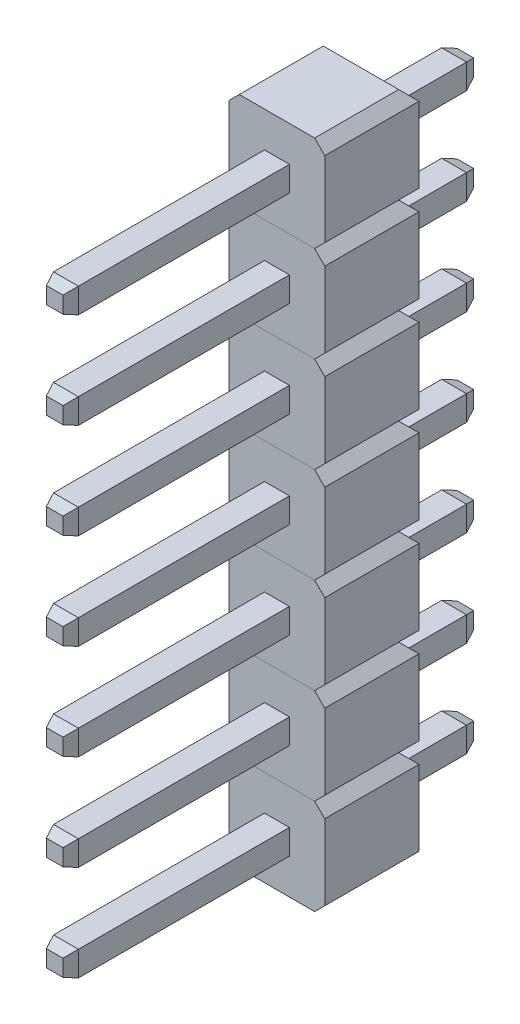
SolidWorks part; units mm, degrees
ref_plane "Front" through (0, 0, 0) normal (0, 0, 1) x (1, 0, 0)
ref_plane "Top" through (0, 0, 0) normal (0, 1, 0) x (1, 0, 0)
ref_plane "Right" through (0, 0, 0) normal (1, 0, 0) x (0, 0, -1)
sketch "Sketch1" plane through (0, 0, 0) normal (0, 0, 1) x (1, 0, 0)
  line L0 (-1.27, 1) -> (-1, 1.27)
  line L1 (-1, -1.27) -> (1, -1.27)
  line L2 (-1.27, -1) -> (-1.27, 1)
  line L3 (-1, 1.27) -> (1, 1.27)
  line L4 (1.27, -1) -> (1.27, 1)
  line L5 (-1.27, -1.27) -> (1.27, 1.27) construction
  line L6 (-1.27, 1.27) -> (1.27, -1.27) construction
  line L7 (0, 0) -> (0, 0.6157) construction
  line L8 (1.27, 1) -> (1, 1.27)
  line L9 (0, 0) -> (-0.572, 0) construction
  line L10 (1.27, -1) -> (1, -1.27)
  line L11 (-1.27, -1) -> (-1, -1.27)
  point P0 (0, 0)
  dimension "D1" = 2.54
  dimension "D2" = 2
extrude "Boss-Extrude1" add sketch "Sketch1" along normal blind 2.5
sketch "Sketch4" plane through (0, 0, 0) normal (0, 1, 0) x (1, 0, 0)
  line L0 (-1.27, 0) -> (1.27, 0)
  line L1 (1.27, 0) -> (1, -0.27)
  line L2 (1, -0.27) -> (-1, -0.27)
  line L3 (-1, -2.5) -> (-1, 0) construction
  line L4 (-1, -0.27) -> (-1.27, 0)
extrude "Cut-Extrude1" cut sketch "Sketch4" against normal through all and the other way through all
sketch "Sketch2" plane through (0, 0, 0) normal (0, 0, 1) x (1, 0, 0)
  line L1 (-0.33, -0.33) -> (0.33, -0.33)
  line L2 (-0.33, -0.33) -> (-0.33, 0.33)
  line L3 (-0.33, 0.33) -> (0.33, 0.33)
  line L4 (0.33, -0.33) -> (0.33, 0.33)
  line L5 (-0.33, -0.33) -> (0.33, 0.33) construction
  line L6 (-0.33, 0.33) -> (0.33, -0.33) construction
  point P0 (0, 0)
  dimension "D1" = 0.66
extrude "Boss-Extrude2" add sketch "Sketch2" against normal blind 2.5 and the other way blind 8.4
chamfer "Chamfer1" distance 0.3 angle 20 8 edges at (0.33, 0, -2.5) (0, -0.33, -2.5) (-0.33, 0, -2.5) (0, 0.33, -2.5) (0, 0.33, 8.4) (0.33, 0, 8.4) (0, -0.33, 8.4) (-0.33, 0, 8.4)
pattern_linear "LPattern1" count 7 spacing 2.54 along (0, 1, 0) of bodies 103
